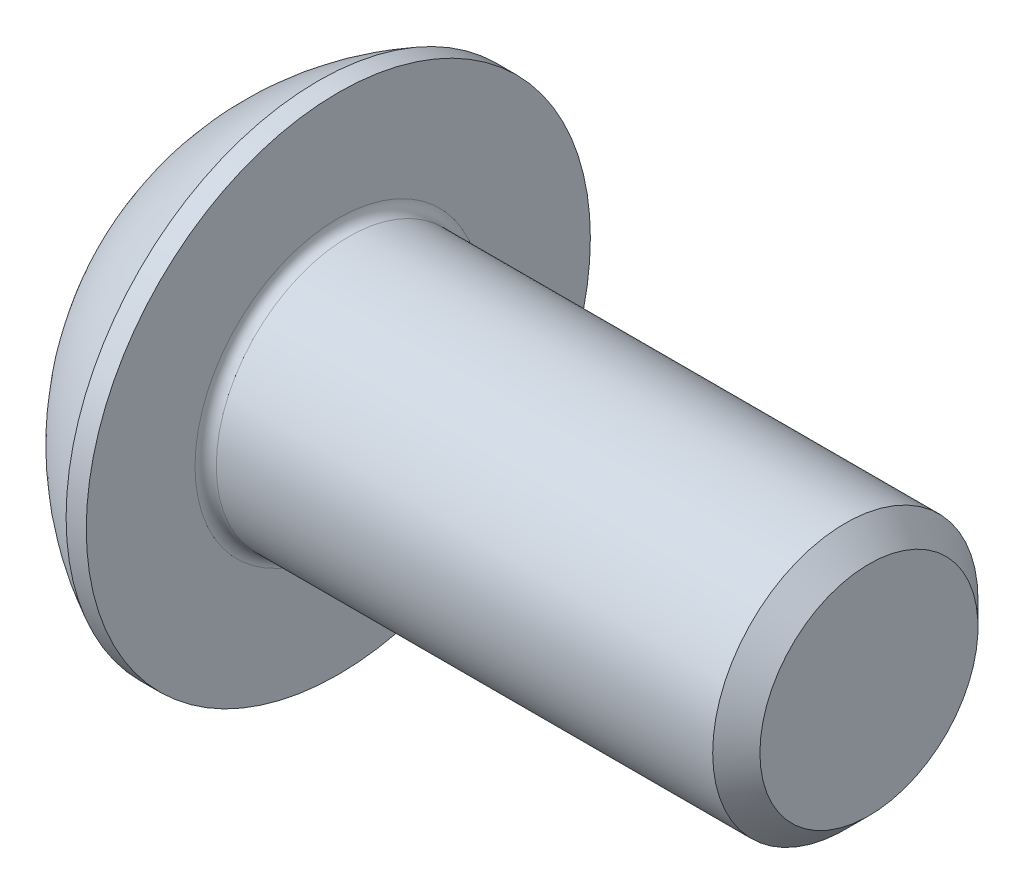
SolidWorks part; units mm, degrees
ref_plane "Plane1" through (0, 0, 0) normal (0, 0, 1) x (1, 0, 0)
ref_plane "Plane2" through (0, 0, 0) normal (0, 1, 0) x (1, 0, 0)
ref_plane "Plane3" through (0, 0, 0) normal (1, 0, 0) x (0, 0, -1)
sketch "BodySke" plane through (0, 0, 0) normal (0, 0, 1) x (1, 0, 0)
  line L0 (12.75, 0) -> (12.75, 2.055)
  line L1 (12.305, 2.5) -> (2.75, 2.5)
  line L2 (2.75, 2.5) -> (2.75, 4.75)
  line L3 (2.75, 4.75) -> (2.37, 4.75)
  line L4 (0, 0) -> (101.6, 0) construction
  line L5 (2.75, -4.75) -> (2.37, -4.75) construction
  line L6 (55.6768, -2.5) -> (2.75, -2.5) construction
  line L7 (12.75, 0) -> (0, 0)
  line L8 (0, 2.375) -> (0, -2.375) construction
  line L9 (0, 0) -> (0, 2.375)
  line L10 (12.75, 2.055) -> (12.305, 2.5)
  line L11 (12.75, -2.055) -> (12.305, -2.5) construction
  line L12 (3.55, 9.525) -> (3.55, -2.5) construction
  line L13 (2.75, 9.525) -> (2.75, -2.5) construction
  arc A1 (0, 2.375) -> (2.37, 4.75) centre (4.755, 0) cw
  dimension "D1" = 4.75
  dimension "Diameter" = 5
  dimension "Length" = 10
  dimension "Head_dia" = 9.5
  dimension "Head_ht" = 2.75
  dimension "Head_side_ht" = 0.38
  dimension "Minor_dia" = 4.11
  dimension "Body_ch_ang" = 45
  dimension "Advance" = 0.8
  dimension "Thread_nom" = 10
revolve "BaseBody" add sketch "BodySke" angle 360 about L4
cosmetic thread "ThreadCosmetic" [suppressed] parameters "Thread_length"=8.4, "Thread_minor"=4.11
fillet "Fillet1" radius 0.2 1 edges at (2.75, 0, 2.5)
sketch "Sketch2" plane through (0, 0, 0) normal (0, 0, 1) x (1, 0, 0)
  line L0 (0, 1.5) -> (1.56, 1.5)
  line L1 (1.56, 1.5) -> (2.426, 0)
  line L3 (2.426, 0) -> (0, 0)
  line L4 (0, 0) -> (0, 1.5)
  line L5 (0, -1.5) -> (1.56, -1.5) construction
  line L6 (0, 0) -> (47.625, 0) construction
  dimension "D2" = 60
  dimension "PreBroach_depth" = 1.56
  dimension "PreBroach_dia" = 3
revolve "PreBroach" cut sketch "Sketch2" angle 360 about L6
sketch "Sketch3" plane through (0, 0, 0) normal (1, 0, 0) x (0, 0, -1)
  line L0 (-1.5, -0.866) -> (-1.5, 0.866)
  line L1 (-1.5, 0.866) -> (0, 1.7321)
  line L2 (0, 1.7321) -> (1.5, 0.866)
  line L3 (1.5, 0.866) -> (1.5, -0.866)
  line L4 (1.5, -0.866) -> (0, -1.7321)
  line L5 (0, -1.7321) -> (-1.5, -0.866)
  dimension "D1" = 1.5
  dimension "D2" = 1.5
  dimension "D3" = 3
  dimension "Hex_size" = 3
extrude "Hex" cut sketch "Sketch3" along normal blind 1.56
sketch "ThdSchSke" plane through (0, 0, 0) normal (0, 0, 1) x (1, 0, 0)
  line L0 (4.35, -2.055) -> (4.0384, -2.5)
  line L1 (4.35, -2.055) -> (4.6616, -2.5)
  line L2 (4.6616, -2.5) -> (4.6616, -3.125)
  line L3 (-3.175, 0) -> (5.1513, 0) construction
  line L5 (4.6616, -3.125) -> (4.0384, -3.125)
  line L6 (4.0384, -3.125) -> (4.0384, -2.5)
  dimension "Thread_minor" = 4.11
  dimension "Diameter" = 5
  dimension "Start" = 4.35
  dimension "SideAngle" = 55
  dimension "VeeAngle" = 70
  dimension "Overcut" = 6.25
revolve "ThreadSchematic" [suppressed] cut sketch "ThdSchSke" angle 360 about L3
pattern_linear "ThdSchPat" [suppressed]
equation "\"D1@BodySke\" = \"Head_dia@BodySke\" * .5"
equation "\"Thread_minor@ThreadCosmetic\" = \"Minor_dia@BodySke\""
equation "\"D1@Sketch3\" = \"Hex_size@Sketch3\" / 2"
equation "\"D2@Sketch3\" = \"D1@Sketch3\""
equation "\"D3@Sketch3\" = \"Hex_size@Sketch3\""
equation "\"Thread_length@ThreadCosmetic\" = ((sgn( (\"Length@BodySke\" - \"Advance@BodySke\" * 2.0) - \"Thread_nom@BodySke\" )-1)*( (\"Length@BodySke\" - \"Advance@BodySke\" * 2.0) - \"Thread_nom@BodySke\" ))/-2+ \"Thread_nom@BodySke\""
equation "\"Thread_minor@ThdSchSke\" = \"Minor_dia@BodySke\""
equation "\"Diameter@ThdSchSke\" = \"Diameter@BodySke\""
equation "\"Overcut@ThdSchSke\" = \"Diameter@BodySke\" * 1.25"
equation "\"Start@ThdSchSke\" = \"Head_ht@BodySke\" + \"Length@BodySke\" - \"Thread_length@ThreadCosmetic\"  '---Non-countersunk---"
equation "\"Num_threads@ThdSchPat\" = int( \"Thread_length@ThreadCosmetic\" / \"Advance@BodySke\" + 0.999 )  + 1"
equation "\"Advance@ThdSchPat\" = \"Thread_length@ThreadCosmetic\" /  (\"Num_threads@ThdSchPat\" - 1) 'relax it"
equation "\"Num_threads@ThdSchPat\" = \"Num_threads@ThdSchPat\" - sgn( \"Num_threads@ThdSchPat\" - 1) '---chamfered tips only---"
